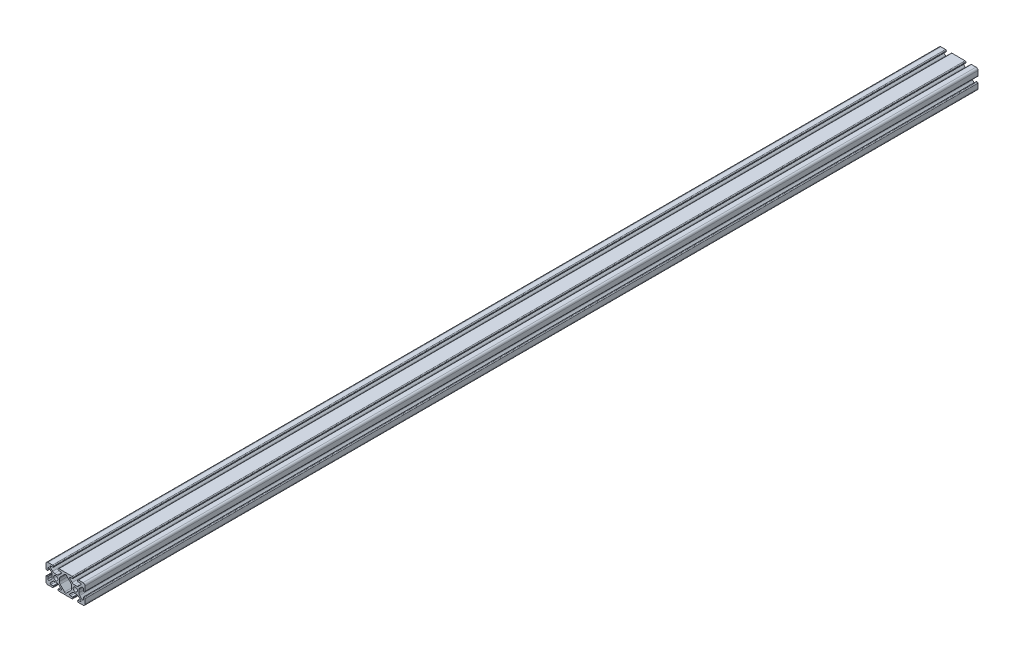
SolidWorks part; units mm, degrees
ref_plane "Front Plane" through (0, 0, 0) normal (0, 0, 1) x (1, 0, 0)
ref_plane "Top Plane" through (0, 0, 0) normal (0, 1, 0) x (1, 0, 0)
ref_plane "Right Plane" through (0, 0, 0) normal (1, 0, 0) x (0, 0, -1)
sketch "Sketch1" plane through (0, 0, 0) normal (0, 0, 1) x (1, 0, 0)
  line L2 (-19.9898, 7.9883) -> (-19.9898, 3.2893)
  line L3 (-17.9832, 9.9949) -> (-13.2842, 9.9949)
  line L4 (-12.4968, 9.2075) -> (-12.4968, 8.4963)
  line L5 (-12.8016, 8.1915) -> (-14.9098, 8.1915)
  line L6 (-15.5025, 6.7606) -> (-13.2477, 4.5058)
  line L7 (-16.7555, 5.5076) -> (-14.5007, 3.2528)
  line L8 (-18.1864, 4.9149) -> (-18.1864, 2.8067)
  line L9 (-18.4912, 2.5019) -> (-19.2024, 2.5019)
  line L11 (-11.1283, 3.6279) -> (-8.8615, 3.6279)
  line L12 (-13.6228, 1.1334) -> (-13.6228, -1.1334)
  line L13 (0, 9.9949) -> (-6.7056, 9.9949)
  line L14 (-7.493, 9.2075) -> (-7.493, 8.4963)
  line L15 (-7.1882, 8.1915) -> (-5.08, 8.1915)
  line L16 (-6.367, 1.1334) -> (-6.367, -1.1334)
  line L17 (-4.4873, 6.7606) -> (-6.7421, 4.5058)
  line L18 (-0.9396, 7.8023) -> (-5.4891, 3.2528)
  line L19 (-18.4912, -2.5019) -> (-19.2024, -2.5019)
  line L20 (-18.1864, -4.9149) -> (-18.1864, -2.8067)
  line L21 (-16.7555, -5.5076) -> (-14.5007, -3.2528)
  line L22 (-15.5025, -6.7606) -> (-13.2477, -4.5058)
  line L23 (-12.8016, -8.1915) -> (-14.9098, -8.1915)
  line L24 (-12.4968, -9.2075) -> (-12.4968, -8.4963)
  line L25 (-17.9832, -9.9949) -> (-13.2842, -9.9949)
  line L26 (-19.9898, -7.9883) -> (-19.9898, -3.2893)
  line L27 (0, -9.9949) -> (-6.7056, -9.9949)
  line L28 (-7.493, -9.2075) -> (-7.493, -8.4963)
  line L29 (-7.1882, -8.1915) -> (-5.08, -8.1915)
  line L30 (-4.4873, -6.7606) -> (-6.7421, -4.5058)
  line L31 (-0.9396, -7.8023) -> (-5.4891, -3.2528)
  line L32 (-11.1283, -3.6279) -> (-8.8615, -3.6279)
  line L34 (11.1283, -3.6279) -> (8.8615, -3.6279)
  line L35 (0.9396, -7.8023) -> (5.4891, -3.2528)
  line L36 (4.4873, -6.7606) -> (6.7421, -4.5058)
  line L37 (7.1882, -8.1915) -> (5.08, -8.1915)
  line L38 (7.493, -9.2075) -> (7.493, -8.4963)
  line L39 (0, -9.9949) -> (6.7056, -9.9949)
  line L40 (19.9898, -7.9883) -> (19.9898, -3.2893)
  line L41 (17.9832, -9.9949) -> (13.2842, -9.9949)
  line L42 (12.4968, -9.2075) -> (12.4968, -8.4963)
  line L43 (12.8016, -8.1915) -> (14.9098, -8.1915)
  line L44 (15.5025, -6.7606) -> (13.2477, -4.5058)
  line L45 (16.7555, -5.5076) -> (14.5007, -3.2528)
  line L46 (18.1864, -4.9149) -> (18.1864, -2.8067)
  line L47 (18.4912, -2.5019) -> (19.2024, -2.5019)
  line L48 (0.9396, 7.8023) -> (5.4891, 3.2528)
  line L49 (4.4873, 6.7606) -> (6.7421, 4.5058)
  line L50 (6.367, 1.1334) -> (6.367, -1.1334)
  line L51 (7.1882, 8.1915) -> (5.08, 8.1915)
  line L52 (7.493, 9.2075) -> (7.493, 8.4963)
  line L53 (0, 9.9949) -> (6.7056, 9.9949)
  line L54 (13.6228, 1.1334) -> (13.6228, -1.1334)
  line L55 (11.1283, 3.6279) -> (8.8615, 3.6279)
  line L56 (18.4912, 2.5019) -> (19.2024, 2.5019)
  line L57 (18.1864, 4.9149) -> (18.1864, 2.8067)
  line L58 (16.7555, 5.5076) -> (14.5007, 3.2528)
  line L59 (15.5025, 6.7606) -> (13.2477, 4.5058)
  line L60 (12.8016, 8.1915) -> (14.9098, 8.1915)
  line L61 (12.4968, 9.2075) -> (12.4968, 8.4963)
  line L62 (17.9832, 9.9949) -> (13.2842, 9.9949)
  line L63 (19.9898, 7.9883) -> (19.9898, 3.2893)
  circle A0 centre (-9.9949, 0) radius 2.1463
  arc A1 (-19.9898, 7.9883) -> (-17.9832, 9.9949) centre (-17.9832, 7.9883) cw
  arc A2 (-16.7555, 5.5076) -> (-18.1864, 4.9149) centre (-17.3482, 4.9149) ccw
  arc A3 (-14.9098, 8.1915) -> (-15.5025, 6.7606) centre (-14.9098, 7.3533) ccw
  arc A4 (-13.2842, 9.9949) -> (-12.4968, 9.2075) centre (-13.2842, 9.2075) cw
  arc A5 (-19.9898, 3.2893) -> (-19.2024, 2.5019) centre (-19.2024, 3.2893) ccw
  arc A6 (-18.1864, 2.8067) -> (-18.4912, 2.5019) centre (-18.4912, 2.8067) cw
  arc A7 (-12.4968, 8.4963) -> (-12.8016, 8.1915) centre (-12.8016, 8.4963) cw
  arc A8 (-11.1283, 3.6279) -> (-13.2477, 4.5058) centre (-11.1283, 6.6251) cw
  arc A9 (-13.6228, 1.1334) -> (-14.5007, 3.2528) centre (-16.62, 1.1334) ccw
  arc A10 (0.9396, 7.8023) -> (-0.9396, 7.8023) centre (0, 6.8627) ccw
  arc A11 (-0.9396, -7.8023) -> (0.9396, -7.8023) centre (0, -6.8627) ccw
  arc A12 (-6.7056, 9.9949) -> (-7.493, 9.2075) centre (-6.7056, 9.2075) ccw
  arc A13 (-7.493, 8.4963) -> (-7.1882, 8.1915) centre (-7.1882, 8.4963) ccw
  arc A14 (-8.8615, 3.6279) -> (-6.7421, 4.5058) centre (-8.8615, 6.6251) ccw
  arc A15 (-6.367, 1.1334) -> (-5.4891, 3.2528) centre (-3.3698, 1.1334) cw
  arc A16 (-5.08, 8.1915) -> (-4.4873, 6.7606) centre (-5.08, 7.3533) cw
  arc A17 (-13.6228, -1.1334) -> (-14.5007, -3.2528) centre (-16.62, -1.1334) cw
  arc A18 (-11.1283, -3.6279) -> (-13.2477, -4.5058) centre (-11.1283, -6.6251) ccw
  arc A19 (-12.4968, -8.4963) -> (-12.8016, -8.1915) centre (-12.8016, -8.4963) ccw
  arc A20 (-18.1864, -2.8067) -> (-18.4912, -2.5019) centre (-18.4912, -2.8067) ccw
  arc A21 (-19.9898, -3.2893) -> (-19.2024, -2.5019) centre (-19.2024, -3.2893) cw
  arc A22 (-13.2842, -9.9949) -> (-12.4968, -9.2075) centre (-13.2842, -9.2075) ccw
  arc A23 (-14.9098, -8.1915) -> (-15.5025, -6.7606) centre (-14.9098, -7.3533) cw
  arc A24 (-16.7555, -5.5076) -> (-18.1864, -4.9149) centre (-17.3482, -4.9149) cw
  arc A25 (-19.9898, -7.9883) -> (-17.9832, -9.9949) centre (-17.9832, -7.9883) ccw
  arc A26 (-5.08, -8.1915) -> (-4.4873, -6.7606) centre (-5.08, -7.3533) ccw
  arc A27 (-6.7056, -9.9949) -> (-7.493, -9.2075) centre (-6.7056, -9.2075) cw
  arc A28 (-7.493, -8.4963) -> (-7.1882, -8.1915) centre (-7.1882, -8.4963) cw
  arc A29 (-8.8615, -3.6279) -> (-6.7421, -4.5058) centre (-8.8615, -6.6251) cw
  arc A30 (-6.367, -1.1334) -> (-5.4891, -3.2528) centre (-3.3698, -1.1334) ccw
  arc A31 (6.367, -1.1334) -> (5.4891, -3.2528) centre (3.3698, -1.1334) cw
  arc A32 (8.8615, -3.6279) -> (6.7421, -4.5058) centre (8.8615, -6.6251) ccw
  arc A33 (7.493, -8.4963) -> (7.1882, -8.1915) centre (7.1882, -8.4963) ccw
  arc A34 (6.7056, -9.9949) -> (7.493, -9.2075) centre (6.7056, -9.2075) ccw
  arc A35 (5.08, -8.1915) -> (4.4873, -6.7606) centre (5.08, -7.3533) cw
  arc A36 (19.9898, -7.9883) -> (17.9832, -9.9949) centre (17.9832, -7.9883) cw
  arc A37 (16.7555, -5.5076) -> (18.1864, -4.9149) centre (17.3482, -4.9149) ccw
  arc A38 (14.9098, -8.1915) -> (15.5025, -6.7606) centre (14.9098, -7.3533) ccw
  arc A39 (13.2842, -9.9949) -> (12.4968, -9.2075) centre (13.2842, -9.2075) cw
  arc A40 (19.9898, -3.2893) -> (19.2024, -2.5019) centre (19.2024, -3.2893) ccw
  arc A41 (18.1864, -2.8067) -> (18.4912, -2.5019) centre (18.4912, -2.8067) cw
  arc A42 (12.4968, -8.4963) -> (12.8016, -8.1915) centre (12.8016, -8.4963) cw
  arc A43 (11.1283, -3.6279) -> (13.2477, -4.5058) centre (11.1283, -6.6251) cw
  arc A44 (13.6228, -1.1334) -> (14.5007, -3.2528) centre (16.62, -1.1334) ccw
  arc A45 (5.08, 8.1915) -> (4.4873, 6.7606) centre (5.08, 7.3533) ccw
  arc A46 (6.367, 1.1334) -> (5.4891, 3.2528) centre (3.3698, 1.1334) ccw
  arc A47 (8.8615, 3.6279) -> (6.7421, 4.5058) centre (8.8615, 6.6251) cw
  arc A48 (7.493, 8.4963) -> (7.1882, 8.1915) centre (7.1882, 8.4963) cw
  arc A49 (6.7056, 9.9949) -> (7.493, 9.2075) centre (6.7056, 9.2075) cw
  arc A50 (13.6228, 1.1334) -> (14.5007, 3.2528) centre (16.62, 1.1334) cw
  arc A51 (11.1283, 3.6279) -> (13.2477, 4.5058) centre (11.1283, 6.6251) ccw
  arc A52 (12.4968, 8.4963) -> (12.8016, 8.1915) centre (12.8016, 8.4963) ccw
  arc A53 (18.1864, 2.8067) -> (18.4912, 2.5019) centre (18.4912, 2.8067) ccw
  arc A54 (19.9898, 3.2893) -> (19.2024, 2.5019) centre (19.2024, 3.2893) cw
  arc A55 (13.2842, 9.9949) -> (12.4968, 9.2075) centre (13.2842, 9.2075) ccw
  arc A56 (14.9098, 8.1915) -> (15.5025, 6.7606) centre (14.9098, 7.3533) cw
  arc A57 (16.7555, 5.5076) -> (18.1864, 4.9149) centre (17.3482, 4.9149) cw
  arc A58 (19.9898, 7.9883) -> (17.9832, 9.9949) centre (17.9832, 7.9883) ccw
  circle A59 centre (9.9949, 0) radius 2.1463
  point P186 (9.9949, 3.6279)
extrude "Boss-Extrude1" add sketch "Sketch1" along normal mid plane 914.4
